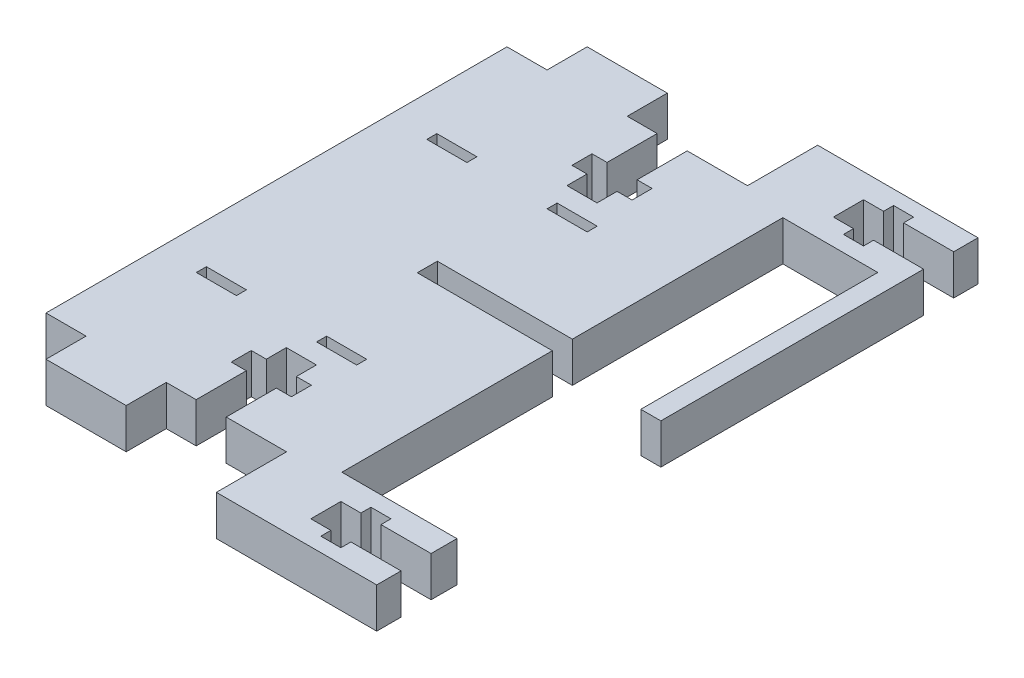
SolidWorks part; units mm, degrees
ref_plane "Front Plane" through (0, 0, 0) normal (0, 0, 1) x (1, 0, 0)
ref_plane "Top Plane" through (0, 0, 0) normal (0, 1, 0) x (1, 0, 0)
ref_plane "Right Plane" through (0, 0, 0) normal (1, 0, 0) x (0, 0, -1)
sketch "Sketch1" plane through (0, 0, 0) normal (0, 1, 0) x (1, 0, 0)
  line L0 (19.05, -19.05) -> (38.1, -19.05)
  line L1 (0, 17.4625) -> (-10.9193, 17.4625) construction
  line L2 (0, 0) -> (0, 34.925)
  line L3 (77.8648, 17.4625) -> (68.3008, 17.4625) construction
  line L4 (38.1, 0) -> (38.1, 34.925)
  line L5 (44.45, -17.4625) -> (74.6898, -17.4625)
  line L6 (38.1, 0) -> (38.1, 34.925)
  line L7 (44.45, 52.3875) -> (74.6898, 52.3875)
  line L8 (77.8648, -15.875) -> (77.8648, 50.8)
  line L9 (38.1, -30.1625) -> (84.2148, -30.1625)
  line L10 (19.05, 53.975) -> (38.1, 53.975)
  line L11 (38.1, 65.0875) -> (84.2148, 65.0875)
  line L12 (84.2148, -30.1625) -> (84.2148, 65.0875)
  line L13 (74.6898, 52.3875) -> (77.8648, 50.8)
  line L14 (77.8648, -15.875) -> (74.6898, -17.4625)
  line L15 (38.1, 0) -> (44.45, -3.6662)
  line L16 (44.45, -3.6662) -> (44.45, -17.4625)
  line L17 (38.1, 34.925) -> (44.45, 38.5912)
  line L18 (44.45, 38.5912) -> (44.45, 52.3875)
  line L21 (0, 34.925) -> (0, 53.975)
  line L22 (0, 53.975) -> (6.35, 53.975)
  line L23 (6.35, 53.975) -> (6.35, 60.325)
  line L24 (6.35, 60.325) -> (19.05, 60.325)
  line L25 (0, 0) -> (0, -19.05)
  line L26 (0, -19.05) -> (6.35, -19.05)
  line L27 (19.05, 53.975) -> (19.05, 60.325)
  line L28 (38.1, -30.1625) -> (38.1, -19.05)
  line L29 (6.35, -19.05) -> (6.35, -25.4)
  line L30 (6.35, -25.4) -> (19.05, -25.4)
  line L31 (19.05, -19.05) -> (19.05, -25.4)
  line L33 (38.1, 65.0875) -> (38.1, 53.975)
  dimension "D1" = 34.925
  dimension "D2" = 38.1
  dimension "D3" = 3.175
  dimension "D4" = 1.5875
  dimension "D5" = 69.85
  dimension "D6" = 12.7
  dimension "D7" = 12.7
  dimension "D8" = 6.35
  dimension "D10" = 1.5875
  dimension "D11" = 3.175
  dimension "D12" = 19.05
  dimension "D13" = 19.05
  dimension "D14" = 30
  dimension "D15" = 30
  dimension "D17" = 6.35
  dimension "D18" = 0
  dimension "D19" = 6.35
  dimension "D20" = 12.7
  dimension "D21" = 6.35
  dimension "D22" = 6.35
  dimension "D23" = 12.7
  dimension "D24" = 6.35
extrude "Boss-Extrude1" add sketch "Sketch1" along normal blind 6.35 contours L11 L33 L10 L27 L24 L23 L22 L21 L2 L25 L26 L29 L30 L31 L0 L28 L9 L12 L17 L18 L7 L13 L8 L14 L5 L16 L15 L4
sketch "Sketch2" plane through (0, 6.35, 0) normal (0, 1, 0) x (1, 0, 0)
  line L0 (0, -19.05) -> (0, 53.975) construction
  line L1 (6.35, 34.925) -> (12.7, 34.925)
  line L2 (6.35, 34.925) -> (6.35, 36.5125)
  line L3 (6.35, 36.5125) -> (12.7, 36.5125)
  line L4 (12.7, 34.925) -> (12.7, 36.5125)
  line L5 (6.35, 0) -> (12.7, 0)
  line L6 (6.35, 0) -> (6.35, -1.5875)
  line L7 (6.35, -1.5875) -> (12.7, -1.5875)
  line L8 (12.7, 0) -> (12.7, -1.5875)
  line L9 (25.4, 34.925) -> (31.75, 34.925)
  line L10 (25.4, 34.925) -> (25.4, 36.5125)
  line L11 (25.4, 36.5125) -> (31.75, 36.5125)
  line L12 (31.75, 34.925) -> (31.75, 36.5125)
  line L13 (25.4, 0) -> (31.75, 0)
  line L14 (25.4, 0) -> (25.4, -1.5875)
  line L15 (25.4, -1.5875) -> (31.75, -1.5875)
  line L16 (31.75, 0) -> (31.75, -1.5875)
  dimension "D1" = 6.35
  dimension "D2" = 6.35
  dimension "D3" = 12.7
  dimension "D4" = 6.35
  dimension "D5" = 6.35
  dimension "D6" = 6.35
  dimension "D7" = 12.7
  dimension "D8" = 6.35
  dimension "D9" = 1.5875
  dimension "D10" = 1.5875
  dimension "D11" = 1.5875
  dimension "D12" = 1.5875
  dimension "D13" = 0
  dimension "D14" = 0
extrude "Cut-Extrude1" cut sketch "Sketch2" against normal blind 6.35
sketch "Sketch3" plane through (0, 6.35, 0) normal (0, 1, 0) x (1, 0, 0)
  line L0 (19.05, 53.975) -> (38.1, 53.975) construction
  line L1 (23.787, 53.975) -> (28.5495, 53.975)
  line L2 (23.787, 53.975) -> (23.787, 39.6875)
  line L3 (23.787, 39.6875) -> (28.5495, 39.6875)
  line L4 (28.5495, 53.975) -> (28.5495, 39.6875)
  line L5 (84.2148, -30.1625) -> (84.2148, 65.0875) construction
  line L6 (21.4058, 46.0375) -> (30.9308, 46.0375)
  line L7 (21.4058, 46.0375) -> (21.4058, 42.8625)
  line L8 (21.4058, 42.8625) -> (30.9308, 42.8625)
  line L9 (30.9308, 46.0375) -> (30.9308, 42.8625)
  line L10 (84.2148, 60.4838) -> (69.9273, 60.4838)
  line L11 (84.2148, 60.4838) -> (84.2148, 55.7213)
  line L12 (84.2148, 55.7213) -> (69.9273, 55.7213)
  line L13 (69.9273, 60.4838) -> (69.9273, 55.7213)
  line L14 (76.2773, -27.1463) -> (76.2773, -19.2088)
  line L15 (73.1023, 62.0713) -> (76.2773, 62.0713)
  line L16 (73.1023, 62.0713) -> (73.1023, 54.1338)
  line L17 (73.1023, 54.1338) -> (76.2773, 54.1338)
  line L18 (76.2773, 62.0713) -> (76.2773, 54.1338)
  line L19 (38.1, 17.4625) -> (77.8648, 17.4625) construction
  line L20 (38.1, 0) -> (38.1, 34.925) construction
  line L21 (77.8648, -15.875) -> (77.8648, 50.8) construction
  line L22 (69.9273, 58.1025) -> (57.9922, 58.1025) construction
  line L23 (73.1023, -19.2088) -> (76.2773, -19.2088)
  line L24 (73.1023, -27.1463) -> (73.1023, -19.2088)
  line L25 (73.1023, -27.1463) -> (76.2773, -27.1463)
  line L26 (69.9273, -25.5588) -> (69.9273, -20.7963)
  line L27 (84.2148, -20.7962) -> (69.9273, -20.7963)
  line L28 (84.2148, -25.5587) -> (84.2148, -20.7962)
  line L29 (84.2148, -25.5587) -> (69.9273, -25.5588)
  line L30 (30.9308, -11.1125) -> (30.9308, -7.9375)
  line L31 (21.4058, -7.9375) -> (30.9308, -7.9375)
  line L32 (21.4058, -11.1125) -> (21.4058, -7.9375)
  line L33 (21.4058, -11.1125) -> (30.9308, -11.1125)
  line L34 (28.5495, -19.05) -> (28.5495, -4.7625)
  line L35 (23.787, -4.7625) -> (28.5495, -4.7625)
  line L36 (23.787, -19.05) -> (23.787, -4.7625)
  line L37 (23.787, -19.05) -> (28.5495, -19.05)
  dimension "D1" = 4.7625
  dimension "D2" = 9.525
  dimension "D3" = 2.3813
  dimension "D4" = 7.9375
  dimension "D5" = 3.175
  dimension "D6" = 3.175
  dimension "D7" = 4.7625
  dimension "D8" = 7.9375
  dimension "D9" = 1.5875
  dimension "D10" = 7.9375
  dimension "D11" = 3.175
  dimension "D12" = 3.175
  dimension "D13" = 40.64
sketch "Sketch4" plane through (0, 6.35, 0) normal (0, 1, 0) x (1, 0, 0)
  line L0 (61.9898, 52.3875) -> (61.9898, -17.4625)
  line L1 (44.45, 52.3875) -> (74.6898, 52.3875) construction
  line L2 (44.45, -17.4625) -> (74.6898, -17.4625) construction
  line L3 (77.8648, -15.875) -> (77.8648, 50.8) construction
  line L4 (61.9898, 52.3875) -> (37.6631, 52.3875)
  line L5 (37.6631, 52.3875) -> (37.6631, -17.4625)
  line L6 (37.6631, -17.4625) -> (61.9898, -17.4625)
  dimension "D1" = 15.875
extrude "Boss-Extrude2" add sketch "Sketch4" along normal blind 6.35 from surface at -6.35 starting at plane "Top Plane"
sketch "Sketch5" plane through (0, 6.35, 0) normal (0, 1, 0) x (1, 0, 0)
  line L0 (61.9898, -17.4625) -> (61.9898, 52.3875) construction
  line L1 (74.6898, 15.875) -> (49.2898, 15.875)
  line L2 (74.6898, 15.875) -> (74.6898, 19.05)
  line L3 (74.6898, 19.05) -> (49.2898, 19.05)
  line L4 (49.2898, 15.875) -> (49.2898, 19.05)
  line L5 (74.6898, 15.875) -> (49.2898, 19.05) construction
  line L6 (74.6898, 19.05) -> (49.2898, 15.875) construction
  line L8 (49.2898, 19.05) -> (23.8898, 19.05)
  line L9 (49.2898, 19.05) -> (49.2898, 15.875)
  line L10 (49.2898, 15.875) -> (23.8898, 15.875)
  line L11 (23.8898, 19.05) -> (23.8898, 15.875)
  point P0 (61.9898, 17.4625)
  dimension "D1" = 3.175
  dimension "D2" = 25.4
  dimension "D3" = 25.4
extrude "Cut-Extrude3" cut sketch "Sketch5" against normal blind 6.35 contours L4 L1 L2 L3 | L8 L11 L10 L4
sketch "Sketch7" plane through (0, 6.35, 0) normal (0, 1, 0) x (1, 0, 0)
  line L0 (38.1, -30.1625) -> (84.2148, -30.1625) construction
  line L1 (81.0398, -30.1625) -> (100.9634, -30.1625)
  line L2 (81.0398, -30.1625) -> (81.0398, 65.0875)
  line L3 (81.0398, 65.0875) -> (100.9634, 65.0875)
  line L4 (100.9634, -30.1625) -> (100.9634, 65.0875)
  line L5 (77.8648, -15.875) -> (77.8648, 50.8) construction
  dimension "D1" = 3.175
extrude "Cut-Extrude4" cut sketch "Sketch7" against normal blind 6.35
sketch "Sketch8" plane through (0, 0, 0) normal (0, -1, 0) x (1, 0, 0)
  line L0 (61.9898, -52.3875) -> (74.6898, -52.3875) construction
  line L1 (45.2817, 17.4625) -> (60.325, 17.4625)
  line L2 (45.2817, 17.4625) -> (45.2817, -52.3875)
  line L3 (45.2817, -52.3875) -> (60.325, -52.3875)
  line L4 (60.325, 17.4625) -> (60.325, -52.3875)
  line L5 (38.1, 30.1625) -> (38.1, 19.05) construction
  dimension "D1" = 22.225
extrude "Cut-Extrude5" cut sketch "Sketch8" against normal blind 6.35
sketch "Sketch9" plane through (0, 0, 0) normal (0, -1, 0) x (1, 0, 0)
  line L0 (38.1, 30.1625) -> (81.0398, 30.1625) construction
  line L1 (60.325, 30.1625) -> (63.5, 30.1625)
  line L2 (60.325, 30.1625) -> (60.325, -65.0875)
  line L3 (60.325, -65.0875) -> (63.5, -65.0875)
  line L4 (63.5, 30.1625) -> (63.5, -65.0875)
  line L5 (38.1, -65.0875) -> (81.0398, -65.0875) construction
  dimension "D1" = 3.175
extrude "Boss-Extrude3" add sketch "Sketch9" against normal blind 6.35 from surface at 0 starting at plane "Top Plane"
sketch "Sketch10" plane through (0, 0, 0) normal (0, -1, 0) x (1, 0, 0)
  line L0 (38.1, 30.1625) -> (81.0398, 30.1625) construction
  line L1 (63.5, 30.1625) -> (81.0398, 30.1625)
  line L2 (63.5, 30.1625) -> (63.5, -65.0875)
  line L3 (63.5, -65.0875) -> (81.0398, -65.0875)
  line L4 (81.0398, 30.1625) -> (81.0398, -65.0875)
  line L5 (38.1, -65.0875) -> (81.0398, -65.0875) construction
extrude "Cut-Extrude7" cut sketch "Sketch10" against normal blind 6.35
extrude "Cut-Extrude8" cut sketch "Sketch3" against normal blind 6.35 contours L4 L3 L2 L1 | L6 L9 L8 L7 | L34 L35 L36 L37 | L31 L30 L33 L32
sketch "Sketch11" plane through (0, 0, 0) normal (0, -1, 0) x (1, 0, 0)
  line L0 (63.5, -65.0875) -> (63.5, 30.1625) construction
  line L1 (63.5, 26.3133) -> (49.2125, 26.3133)
  line L2 (63.5, 26.3133) -> (63.5, 21.5508)
  line L3 (63.5, 21.5508) -> (49.2125, 21.5508)
  line L4 (49.2125, 26.3133) -> (49.2125, 21.5508)
  line L5 (60.325, -52.3875) -> (60.325, 17.4625) construction
  line L6 (52.3875, 27.9008) -> (55.5625, 27.9008)
  line L7 (52.3875, 27.9008) -> (52.3875, 19.9633)
  line L8 (52.3875, 19.9633) -> (55.5625, 19.9633)
  line L9 (55.5625, 27.9008) -> (55.5625, 19.9633)
  line L10 (60.325, -17.4625) -> (54.7157, -17.4625)
  line L11 (60.325, -17.4625) -> (60.325, -17.3657)
  line L12 (60.325, -17.3657) -> (54.7157, -17.3657)
  line L13 (54.7157, -17.4625) -> (54.7157, -17.3657)
  line L14 (55.5625, -62.8258) -> (55.5625, -54.8883)
  line L15 (52.3875, -54.8883) -> (55.5625, -54.8883)
  line L16 (52.3875, -62.8258) -> (52.3875, -54.8883)
  line L17 (52.3875, -62.8258) -> (55.5625, -62.8258)
  line L18 (49.2125, -61.2383) -> (49.2125, -56.4758)
  line L19 (63.5, -56.4758) -> (49.2125, -56.4758)
  line L20 (63.5, -61.2383) -> (63.5, -56.4758)
  line L21 (63.5, -61.2383) -> (49.2125, -61.2383)
  dimension "D1" = 4.7625
  dimension "D2" = 7.9375
  dimension "D3" = 1.5875
  dimension "D4" = 7.9375
  dimension "D5" = 3.175
  dimension "D6" = 3.175
extrude "Cut-Extrude9" cut sketch "Sketch11" against normal blind 6.35 contours L1 L4 L3 L2 | L6 L9 L8 L7 | L18 L19 L20 L21 | L15 L14 L17 L16
sketch "Sketch14" plane through (0, 6.35, 0) normal (0, 1, 0) x (1, 0, 0)
  line L1 (60.325, -17.4625) -> (74.9004, -17.4625)
  line L2 (60.325, -17.4625) -> (60.325, 14.848)
  line L3 (60.325, 14.848) -> (74.9004, 14.848)
  line L4 (74.9004, -17.4625) -> (74.9004, 14.848)
extrude "Cut-Extrude11" cut sketch "Sketch14" against normal blind 6.35
